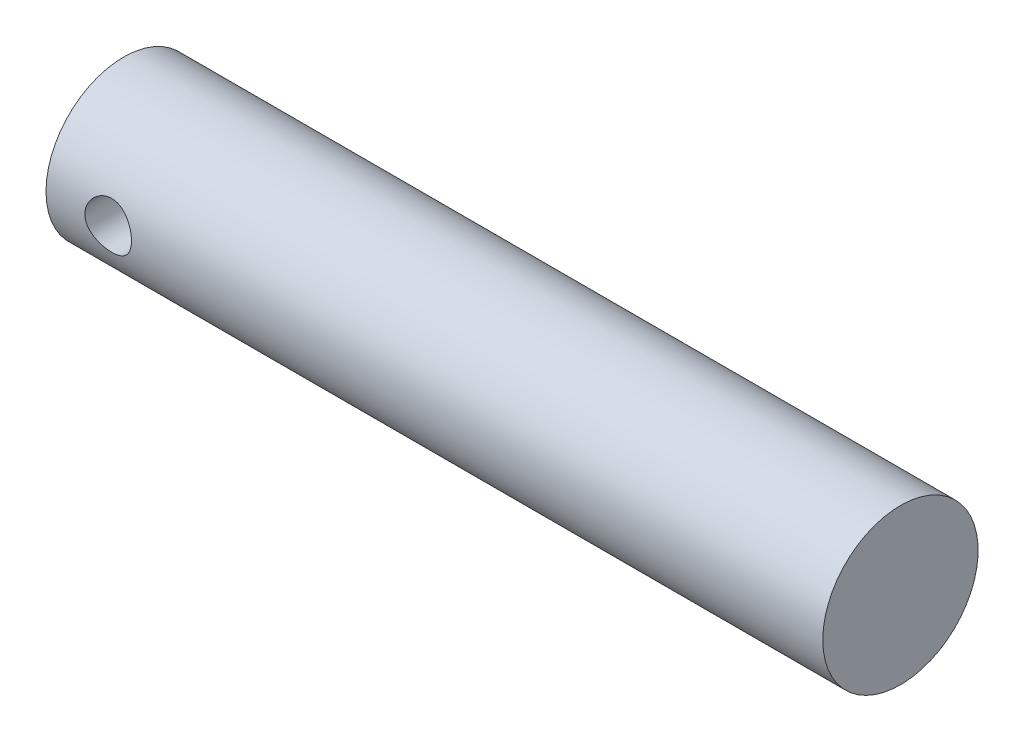
SolidWorks part; units mm, degrees
ref_plane "Ebene vorne" through (0, 0, 0) normal (0, 0, 1) x (1, 0, 0)
ref_plane "Ebene oben" through (0, 0, 0) normal (0, 1, 0) x (1, 0, 0)
ref_plane "Ebene rechts" through (0, 0, 0) normal (1, 0, 0) x (0, 0, -1)
sketch "Skizze1" plane through (0, 0, 0) normal (0, 0, 1) x (1, 0, 0)
  line L1 (0, 0) -> (100, 0)
  line L2 (0, 0) -> (0, 10)
  line L3 (0, 10) -> (100, 10)
  line L4 (100, 0) -> (100, 10)
  dimension "D1" = 10
  dimension "D2" = 100
revolve "Rotation1" add sketch "Skizze1" angle 360 about L1
sketch "Skizze2" plane through (0, 0, 0) normal (0, 0, 1) x (1, 0, 0)
  circle A0 centre (8, 0) radius 3
  dimension "D1" = 6
  dimension "D2" = 8
extrude "Schnitt-Linear austragen1" cut sketch "Skizze2" against normal up to next and the other way up to next
